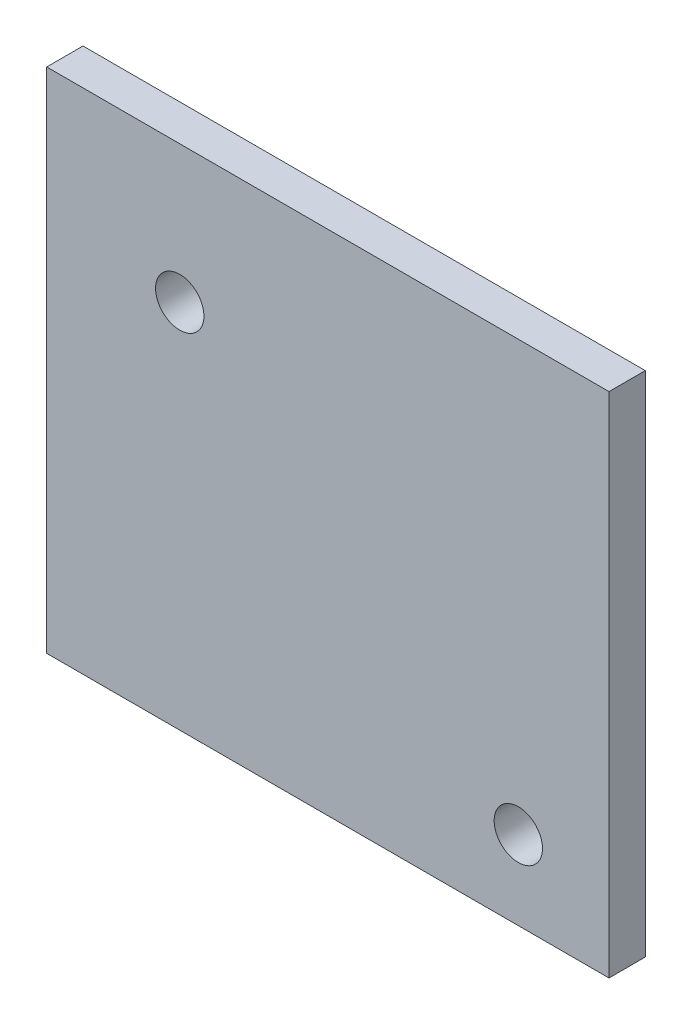
SolidWorks part; units mm, degrees
ref_plane "Front Plane" through (0, 0, 0) normal (0, 0, 1) x (1, 0, 0)
ref_plane "Top Plane" through (0, 0, 0) normal (0, 1, 0) x (1, 0, 0)
ref_plane "Right Plane" through (0, 0, 0) normal (1, 0, 0) x (0, 0, -1)
sketch "Sketch1" plane through (0, 0, 0) normal (0, 0, 1) x (1, 0, 0)
  line L0 (-21.686, 20.907) -> (24.814, 20.907)
  line L1 (-21.686, 20.907) -> (-21.686, -21.093)
  line L2 (-21.686, -21.093) -> (24.814, -21.093)
  line L3 (24.814, 20.907) -> (24.814, -21.093)
  line L4 (-21.686, 442.907) -> (-21.686, -457.093) construction
  line L5 (28.314, -457.093) -> (28.314, 442.907) construction
  circle A0 centre (-10.686, 9.5555) radius 2 construction
  circle A1 centre (-10.686, 9.5555) radius 2
  circle A2 centre (17.314, -14.5729) radius 2 construction
  circle A3 centre (17.314, -14.5729) radius 2
  dimension "D1" = 3.5
  dimension "D2" = 42
extrude "Boss-Extrude1" add sketch "Sketch1" along normal blind 3
